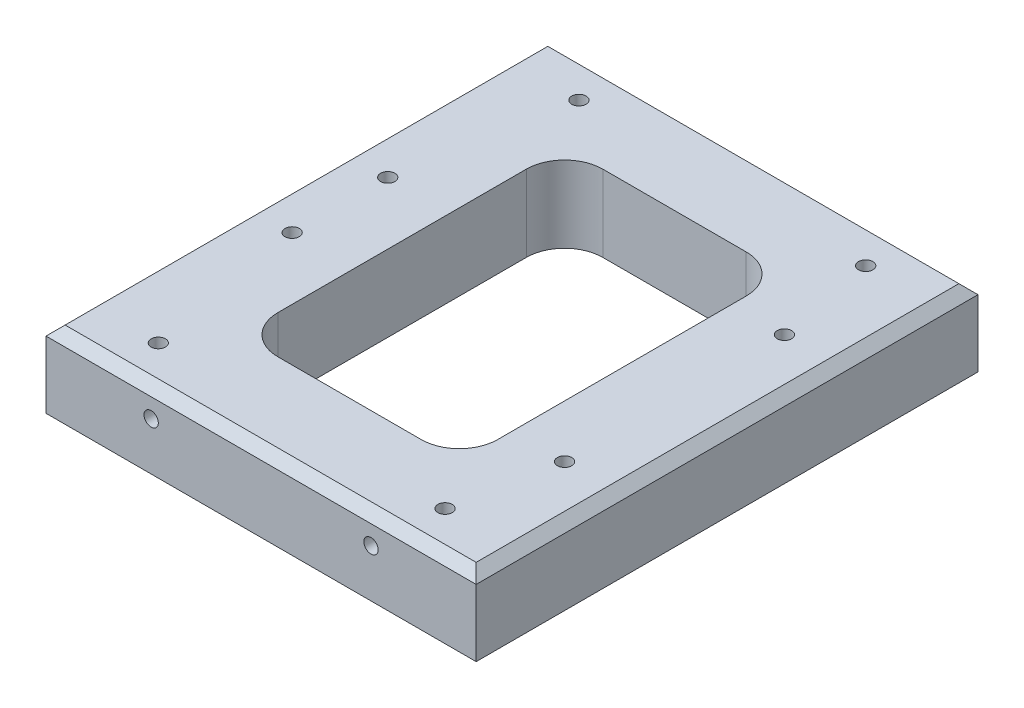
SolidWorks part; units mm, degrees
ref_plane "Front Plane" through (0, 0, 0) normal (0, 0, 1) x (1, 0, 0)
ref_plane "Top Plane" through (0, 0, 0) normal (0, 1, 0) x (1, 0, 0)
ref_plane "Right Plane" through (0, 0, 0) normal (1, 0, 0) x (0, 0, -1)
sketch "Sketch1" plane through (0, 0, 0) normal (0, 1, 0) x (1, 0, 0)
  line L1 (-45, 52.5) -> (45, 52.5)
  line L2 (-45, 52.5) -> (-45, -52.5)
  line L3 (-45, -52.5) -> (45, -52.5)
  line L4 (45, 52.5) -> (45, -52.5)
  line L7 (-15, -34) -> (15, -34)
  line L8 (-23, -26) -> (-23, 26)
  line L9 (-15, 34) -> (15, 34)
  line L10 (23, -26) -> (23, 26)
  arc A0 (-15, -34) -> (-23, -26) centre (-15, -26) cw
  arc A1 (15, -34) -> (23, -26) centre (15, -26) ccw
  arc A2 (15, 34) -> (23, 26) centre (15, 26) cw
  arc A3 (-23, 26) -> (-15, 34) centre (-15, 26) cw
  circle A4 centre (-30, 44) radius 1.5
  circle A5 centre (30, 44) radius 1.5
  circle A6 centre (30, -44) radius 1.5
  circle A7 centre (-30, -44) radius 1.5
  circle A8 centre (-36, -10) radius 1.5
  circle A9 centre (-36, 10) radius 1.5
  circle A10 centre (34, 23) radius 1.5
  circle A11 centre (34, -23) radius 1.5
  point P17 (0, 0)
  dimension "D1" = 8
extrude "Boss-Extrude1" add sketch "Sketch1" along normal blind 16
chamfer "Chamfer1" distance 2 angle 45 4 edges at (-45, 16, 0) (0, 16, -52.5) (45, 16, 0) (0, 16, 52.5)
sketch "Sketch2" plane through (0, 0, 52.5) normal (0, 0, 1) x (1, 0, 0)
  circle A0 centre (-23, 10) radius 1.5
  circle A1 centre (23, 10) radius 1.5
extrude "Cut-Extrude1" cut sketch "Sketch2" against normal blind 10
mirror "Mirror1" about plane through (0, 0, 0) normal (0, 0, 1) of "Cut-Extrude1"
